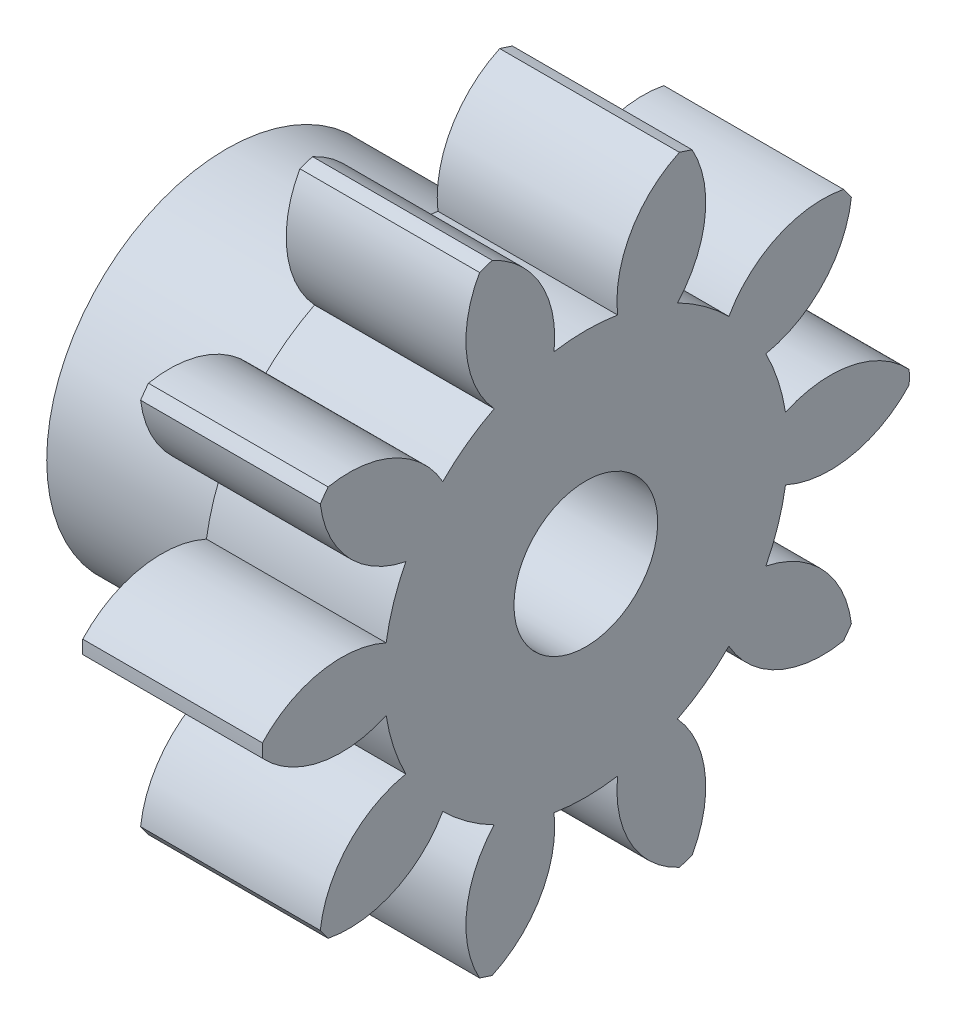
SolidWorks part; units mm, degrees
ref_plane "Plane1" through (0, 0, 0) normal (0, 0, 1) x (1, 0, 0)
ref_plane "Plane2" through (0, 0, 0) normal (0, 1, 0) x (1, 0, 0)
ref_plane "Plane3" through (0, 0, 0) normal (1, 0, 0) x (0, 0, -1)
sketch "HoldingSke" plane through (0, 0, 0) normal (0, 1, 0) x (1, 0, 0)
  line L0 (0, 0) -> (0.3283, -0.0579)
  line L1 (-15, 0) -> (100, 0) construction
  line L2 (0, 0) -> (-2.1039, 2.3779)
  line L3 (0, 0) -> (-11.863, 4.5341)
  line L4 (0, 0) -> (8.5048, 1.4996)
  line L5 (0, 0) -> (-18.7391, -6.9891)
  line L6 (0, 0) -> (-8.2896, -5.593)
  line L7 (-2.1039, 2.3779) -> (2.2011, 21.9091)
  line L8 (-76.2, 54.61) -> (-75.2, 54.61)
  line L9 (-71.009, 38.7566) -> (-53.1078, 45.2721)
  line L10 (-76.2, 71.12) -> (104.1128, 71.12)
  line L11 (0, 0) -> (-10, 0)
  line L12 (-76.2, 101.6) -> (-76.093, 101.6)
  line L13 (24.9733, 27.94) -> (52.9518, 28.4284)
  line L14 (24.9733, 27.94) -> (24.9743, 27.94)
  line L15 (24.9733, 27.94) -> (100.4006, 29.5858)
  line L16 (-63.627, -3) -> (-12.827, -3)
  circle A0 centre (0, 0) radius 3.5
  circle A1 centre (0, 0) radius 10
  circle A2 centre (0, 0) radius 10
  circle A3 centre (0, 0) radius 3.5
  dimension "MHD" = 20
  dimension "Hub_dia" = 20
  dimension "Bore" = 7
  dimension "MBD" = 7
  dimension "Num_teeth" = 10
  dimension "Pitch" = 0.3333
  dimension "Overall_len" = 20
  dimension "Show_teeth" = 10
  dimension "Thickness" = 10
  dimension "OAL" = 20.0001
  dimension "T_dim" = 1
  dimension "Ap" = 20
  dimension "H" = 19.05
  dimension "Pitch_radius" = 180.3128
  dimension "Width" = 10
  dimension "Backlash" = 0.107
  dimension "Addendum_fac" = 1
  dimension "Dedendum_fac" = 1.25
  dimension "Clearance_fac" = 0.25
  dimension "Dedendum_add" = 0.001
  dimension "Module" = 3
sketch "BasProSke" plane through (0, 0, 0) normal (0, 1, 0) x (1, 0, 0)
  line L0 (-10, 0) -> (60, 0) construction
  line L1 (0, 0) -> (0, 18)
  line L2 (0, 0) -> (10, 0)
  line L3 (10, 0) -> (10, 18)
  line L4 (10, 18) -> (0, 18)
  dimension "Thickness" = 10
  dimension "Diameter" = 36
revolve "Base-Revolve" add sketch "BasProSke" angle 360 about L0
sketch "TooCutSke" plane through (0, 0, 0) normal (1, 0, 0) x (0, 0, -1)
  line L1 (0, 0) -> (0, 107) construction
  line L2 (0, 0) -> (-2.5334, 14.7845) construction
  line L3 (0, 0) -> (-9.174, 28.2345) construction
  line L4 (-2.5334, 14.7845) -> (-4.587, 14.1173) construction
  arc A0 (1.7689, 11.109) -> (-1.7689, 11.109) centre (0, 0) ccw
  arc A1 (5.2426, 17.2462) -> (-5.2426, 17.2462) centre (0, 0) ccw
  circle A2 centre (0, 0) radius 15 construction
  circle A3 centre (0, 0) radius 14.0954 construction
  arc A4 (-1.7689, 11.109) -> (-5.2426, 17.2462) centre (-7.7306, 11.7863) ccw
  arc A5 (5.2426, 17.2462) -> (1.7689, 11.109) centre (7.7306, 11.7863) ccw
  dimension "Root_dia" = 22.498
  dimension "Overcut_dia" = 36.0508
  dimension "Pitch_dia" = 30
  dimension "Base_dia" = 28.1908
  dimension "Flank_rad" = 6
  dimension "Half_ang" = 18
  dimension "Half_CT" = 2.1593
extrude "ToothCut" cut sketch "TooCutSke" along normal through all
fillet "Breaks" [suppressed] radius 0.06
fillet "RootFillets" [suppressed] radius 0.751
pattern_circular "TeethCuts" count 10 every 36 about axis through (-10, 0, 0) along (1, 0, 0) of "ToothCut", "RootFillets", "Breaks"
sketch "HubNeaOneSke" plane through (0, 0, 0) normal (-1, 0, 0) x (0, 0, 1)
  circle A0 centre (0, 0) radius 10
  dimension "Diameter" = 20
extrude "HubNearOne" add sketch "HubNeaOneSke" along normal blind 10.0001
sketch "HubNeaBotSke" plane through (0, 0, 0) normal (-1, 0, 0) x (0, 0, 1)
  circle A0 centre (0, 0) radius 10
  dimension "Diameter" = 20
extrude "HubNearBoth" [suppressed] add sketch "HubNeaBotSke" along normal blind 5
ref_plane "FarPln" through (10, 0, 0) normal (1, 0, 0) x (0, 0, -1)
sketch "HubFarSke" plane through (10, 0, 0) normal (1, 0, 0) x (0, 0, -1)
  circle A0 centre (0, 0) radius 10
  dimension "Diameter" = 20
extrude "HubFar" [suppressed] add sketch "HubFarSke" along normal blind 5
sketch "BorSke" plane through (0, 0, 0) normal (1, 0, 0) x (0, 0, -1)
  circle A0 centre (0, 0) radius 3.5
  dimension "Diameter" = 7
extrude "Bore" cut sketch "BorSke" along normal mid plane 40.0001
sketch "KeySke" plane through (0, 0, 0) normal (1, 0, 0) x (0, 0, -1)
  line L0 (-1, 0) -> (-1, 4.5)
  line L1 (-1, 4.5) -> (1, 4.5)
  line L2 (1, 4.5) -> (1, 0)
  line L3 (0, 0) -> (0, 34) construction
  line L4 (-1, 0) -> (1, 0)
  dimension "Offset" = 4.5
  dimension "Width" = 2
extrude "Keyway" [suppressed] cut sketch "KeySke" along normal mid plane 40.0001
pattern_circular "Keyway2" [suppressed] count 2 every 90 about axis through (-10, 0, 0) along (1, 0, 0)
sketch "Sketch1" plane through (-10.0001, 0, 0) normal (-1, 0, 0) x (0, 0, 1)
  line L1 (7.7942, 0) -> (3.8971, 6.75)
  line L2 (3.8971, 6.75) -> (-3.8971, 6.75)
  line L3 (-3.8971, 6.75) -> (-7.7942, 0)
  line L4 (-7.7942, 0) -> (-3.8971, -6.75)
  line L5 (-3.8971, -6.75) -> (3.8971, -6.75)
  line L6 (3.8971, -6.75) -> (7.7942, 0)
  circle A0 centre (0, 0) radius 6.75 construction
  dimension "D1" = 13.5
extrude "Cut-Extrude1" cut sketch "Sketch1" against normal blind 6
sketch "Sketch2" plane through (-4.0001, 0, 0) normal (-1, 0, 0) x (0, 0, 1)
  circle A0 centre (0, 0) radius 4
extrude "Cut-Extrude2" cut sketch "Sketch2" against normal through all
sketch "Sketch3" plane through (0, 0, 0) normal (0, 1, 0) x (1, 0, 0)
  line L0 (-10.0001, 0) -> (-7.0001, 0) construction
  line L1 (-10.0001, 10) -> (-10.0001, -10) construction
  circle A0 centre (-7.0001, 0) radius 2.25
  dimension "D1" = 4.5
  dimension "D2" = 3
extrude "Cut-Extrude3" cut sketch "Sketch3" against normal through all
equation "' \"Module@HoldingSke\" = 6.35"
equation "' \"Num_teeth@HoldingSke\" = 12"
equation "' \"Ap@HoldingSke\" =  20"
equation "' \"Ap@HoldingSke\" = 20"
equation "' \"Width@HoldingSke\" = 0.5 * 25.4"
equation "' \"Hub_dia@HoldingSke\"= 1 * 25.4"
equation "' \"Hub_dia@HoldingSke\" = 1 * 25.4"
equation "' \"Overall_len@HoldingSke\" = 1.0 * 25.4"
equation "' \"Bore@HoldingSke\" = 0.75 * 25.4"
equation "' \"T_dim@HoldingSke\" = 0.1 * 25.4"
equation "' \"Width@KeySke\" = 0.25 * 25.4"
equation "' \"Show_teeth@HoldingSke\" = 13"
equation "' \"Backlash@HoldingSke\" = 0.009 * 25.4"
equation "' \"Addendum_fac@HoldingSke\" = 1.0"
equation "' \"Dedendum_fac@HoldingSke\" = 1.25"
equation "' \"Dedendum_add@HoldingSke\" = 0.00005 * 25.4"
equation "' \"Clearance_fac@HoldingSke\" = 0.25"
equation "\"Pitch@HoldingSke\" = 1 / \"Module@HoldingSke\""
equation "\"Overcut_dia@TooCutSke\" = (\"Num_teeth@HoldingSke\" + 2 * \"Addendum_fac@HoldingSke\") / \"Pitch@HoldingSke\" + 0.002 * 25.4"
equation "\"Pitch_dia@TooCutSke\" = \"Num_teeth@HoldingSke\" / \"Pitch@HoldingSke\""
equation "\"Base_dia@TooCutSke\" = \"Num_teeth@HoldingSke\" / \"Pitch@HoldingSke\" * cos((\"Ap@HoldingSke\"  * 3.14159265 / 180))"
equation "\"Root_dia@TooCutSke\" = (\"Num_teeth@HoldingSke\" + 2) / \"Pitch@HoldingSke\" - 2 * (\"Addendum_fac@HoldingSke\" + \"Dedendum_fac@HoldingSke\") / \"Pitch@HoldingSke\" - \"Dedendum_add@HoldingSke\" * 2"
equation "\"Half_ang@TooCutSke\" = 180 / \"Num_teeth@HoldingSke\""
equation "\"Half_CT@TooCutSke\" = \"Num_teeth@HoldingSke\" / \"Pitch@HoldingSke\" * sin((3.14159265 / 2 / \"Num_teeth@HoldingSke\")) / 2 - 7 * \"Backlash@HoldingSke\" / 4"
equation "\"Flank_rad@TooCutSke\" = \"Num_teeth@HoldingSke\" / \"Pitch@HoldingSke\" / 5"
equation "\"Radius@RootFillets\" = \"Clearance_fac@HoldingSke\" / \"Pitch@HoldingSke\" + \"Dedendum_add@HoldingSke\""
equation "\"Break_rad@Breaks\" = 0.02 / \"Pitch@HoldingSke\""
equation "\"Thickness@HoldingSke\" = \"Width@HoldingSke\""
equation "\"OAL@HoldingSke\" = \"Thickness@HoldingSke\""
equation "\"MHD@HoldingSke\" = (\"Num_teeth@HoldingSke\" + 2) / \"Pitch@HoldingSke\" - 2 * (\"Addendum_fac@HoldingSke\" + \"Dedendum_fac@HoldingSke\")  / \"Pitch@HoldingSke\" - \"Dedendum_add@HoldingSke\" * 2"
equation "\"MBD@HoldingSke\" = (\"Num_teeth@HoldingSke\" + 2) / \"Pitch@HoldingSke\" - 2 * (\"Addendum_fac@HoldingSke\" + \"Dedendum_fac@HoldingSke\")  / \"Pitch@HoldingSke\" - \"Dedendum_add@HoldingSke\" * 2 - 0.002 * 25.4"
equation "\"MHD@HoldingSke\" = ((sgn( \"MHD@HoldingSke\" - \"Hub_dia@HoldingSke\" )-1)*( \"MHD@HoldingSke\" - \"Hub_dia@HoldingSke\" ))/-2+ \"Hub_dia@HoldingSke\""
equation "\"MBD@HoldingSke\" = ((sgn( \"MBD@HoldingSke\" - \"Bore@HoldingSke\" )-1)*( \"MBD@HoldingSke\" - \"Bore@HoldingSke\" ))/-2+ \"Bore@HoldingSke\""
equation "\"OAL@HoldingSke\" = ((sgn( \"OAL@HoldingSke\" - \"Overall_len@HoldingSke\" )+1)*( \"OAL@HoldingSke\" - \"Overall_len@HoldingSke\" ))/2 + \"Overall_len@HoldingSke\" + 0.000002 * 25.4"
equation "\"Num_teeth@TeethCuts\" = int( \"Show_teeth@HoldingSke\" ) + 1"
equation "\"Num_teeth@TeethCuts\" = ((sgn( \"Num_teeth@TeethCuts\" - \"Num_teeth@HoldingSke\" )-1)*( \"Num_teeth@TeethCuts\" - \"Num_teeth@HoldingSke\" ))/-2+ \"Num_teeth@HoldingSke\""
equation "\"Num_teeth@TeethCuts\" = ((sgn( \"Num_teeth@TeethCuts\" - 2.0)+1)*( \"Num_teeth@TeethCuts\" - 2.0))/2 +2.0"
equation "\"Angle@TeethCuts\" = 360.0 / \"Num_teeth@HoldingSke\""
equation "\"Diameter@BasProSke\" = (\"Num_teeth@HoldingSke\" + 2 * \"Addendum_fac@HoldingSke\") / \"Pitch@HoldingSke\""
equation "\"Thickness@BasProSke\"  = \"Thickness@HoldingSke\""
equation "' \"Fillet_rad@BasProSke\" =  \"Thickness@HoldingSke\" * 0.05"
equation "' \"Fillet_rad@BasProSke\" = \"Thickness@HoldingSke\" * 0.05"
equation "\"MHD@HoldingSke\" = ((sgn( \"MHD@HoldingSke\" - \"Root_dia@TooCutSke\" )-1)*( \"MHD@HoldingSke\" - \"Root_dia@TooCutSke\" ))/-2+ \"Root_dia@TooCutSke\""
equation "\"Diameter@HubNeaOneSke\" = \"MHD@HoldingSke\""
equation "\"Length@HubNearOne\" = \"OAL@HoldingSke\" - \"Thickness@BasProSke\""
equation "\"Diameter@HubNeaBotSke\" = \"MHD@HoldingSke\""
equation "\"Length@HubNearBoth\" = ( \"OAL@HoldingSke\" - \"Thickness@BasProSke\" ) / 2.0"
equation "\"Thickness@FarPln\" = \"Thickness@BasProSke\""
equation "\"Diameter@HubFarSke\" = \"MHD@HoldingSke\""
equation "\"Length@HubFar\" = ( \"OAL@HoldingSke\" - \"Thickness@BasProSke\" ) / 2.0"
equation "\"Diameter@BorSke\" = \"MBD@HoldingSke\""
equation "\"D1@Bore\" = \"OAL@HoldingSke\" * 2.0"
equation "\"D1@Keyway\" = \"OAL@HoldingSke\" * 2.0"
equation "\"Offset@KeySke\" = \"T_dim@HoldingSke\" + \"MBD@HoldingSke\" / 2.0"
